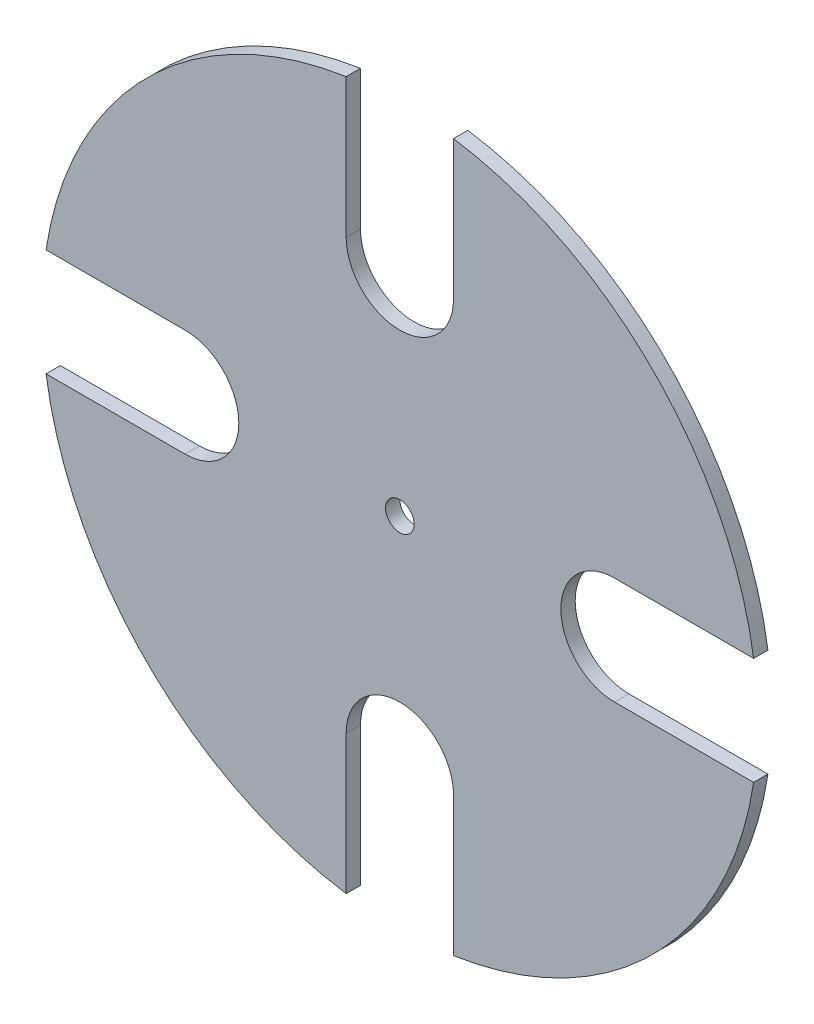
SolidWorks part; units mm, degrees
ref_plane "Front Plane" through (0, 0, 0) normal (0, 0, 1) x (1, 0, 0)
ref_plane "Top Plane" through (0, 0, 0) normal (0, 1, 0) x (1, 0, 0)
ref_plane "Right Plane" through (0, 0, 0) normal (1, 0, 0) x (0, 0, -1)
sketch "Sketch1" plane through (0, 0, 0) normal (0, 0, 1) x (1, 0, 0)
  circle A0 centre (0, 0) radius 100
  circle A1 centre (0, 0) radius 4
  dimension "D1" = 200
  dimension "8" = 8
extrude "Boss-Extrude1" add sketch "Sketch1" along normal blind 4
sketch "Sketch2" plane through (0, 0, 4) normal (0, 0, 1) x (1, 0, 0)
  line L0 (15, 60) -> (15, 143.3431)
  line L1 (-15, 60) -> (-15, 134.0797)
  arc A0 (-15, 60) -> (15, 60) centre (0, 60) ccw
  circle A1 centre (0, 0) radius 100 construction
  dimension "D1" = 15
  dimension "D2" = 40
extrude "Cut-Extrude2" cut sketch "Sketch2" against normal blind 4 and the other way through all flip side to cut
pattern_circular "CirPattern14" count 4 over 360 about axis through (0, 0, 0) along (0, 0, 1) of "Cut-Extrude2"
